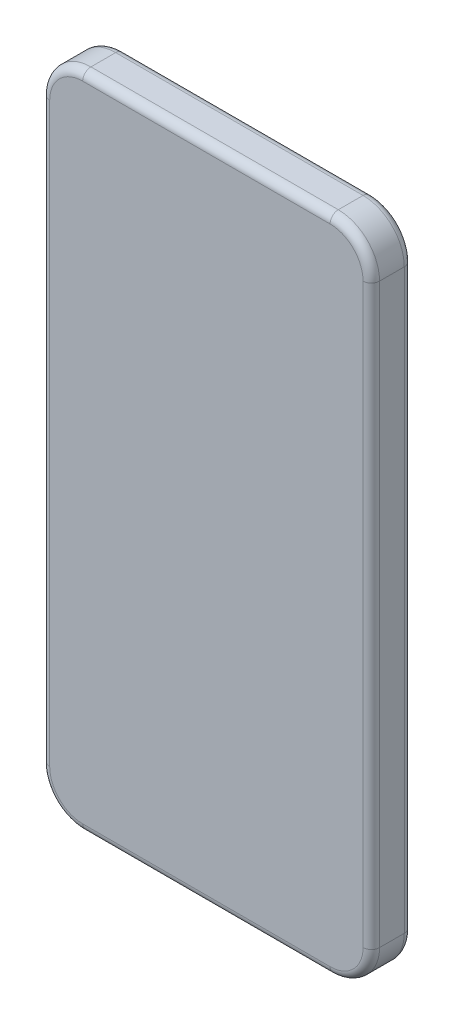
SolidWorks part; units mm, degrees
ref_plane "Front Plane" through (0, 0, 0) normal (0, 0, 1) x (1, 0, 0)
ref_plane "Top Plane" through (0, 0, 0) normal (0, 1, 0) x (1, 0, 0)
ref_plane "Right Plane" through (0, 0, 0) normal (1, 0, 0) x (0, 0, -1)
sketch "Sketch1" plane through (0, 0, 0) normal (0, 0, 1) x (1, 0, 0)
  line L1 (30, 80) -> (-30, 80)
  line L2 (40, 70) -> (40, -70)
  line L3 (30, -80) -> (-30, -80)
  line L4 (-40, 70) -> (-40, -70)
  line L5 (40, 80) -> (-40, -80) construction
  line L6 (40, -80) -> (-40, 80) construction
  arc A0 (40, -70) -> (30, -80) centre (30, -70) cw
  arc A1 (-30, -80) -> (-40, -70) centre (-30, -70) cw
  arc A2 (-30, 80) -> (-40, 70) centre (-30, 70) ccw
  arc A3 (30, 80) -> (40, 70) centre (30, 70) cw
  point P0 (0, 0)
  dimension "D3" = 10
  dimension "D1" = 80
  dimension "D2" = 160
extrude "Boss-Extrude1" add sketch "Sketch1" along normal blind 10
fillet "Fillet1" radius 2 16 edges at (40, 0, 0) (37.0711, 77.0711, 0) (0, 80, 0) (-37.0711, 77.0711, 0) (-40, 0, 0) (-37.0711, -77.0711, 0) (0, -80, 0) (37.0711, -77.0711, 0) (0, -80, 10) (-37.0711, -77.0711, 10) (-40, 0, 10) (-37.0711, 77.0711, 10) (0, 80, 10) (37.0711, 77.0711, 10) (40, 0, 10) (37.0711, -77.0711, 10)
